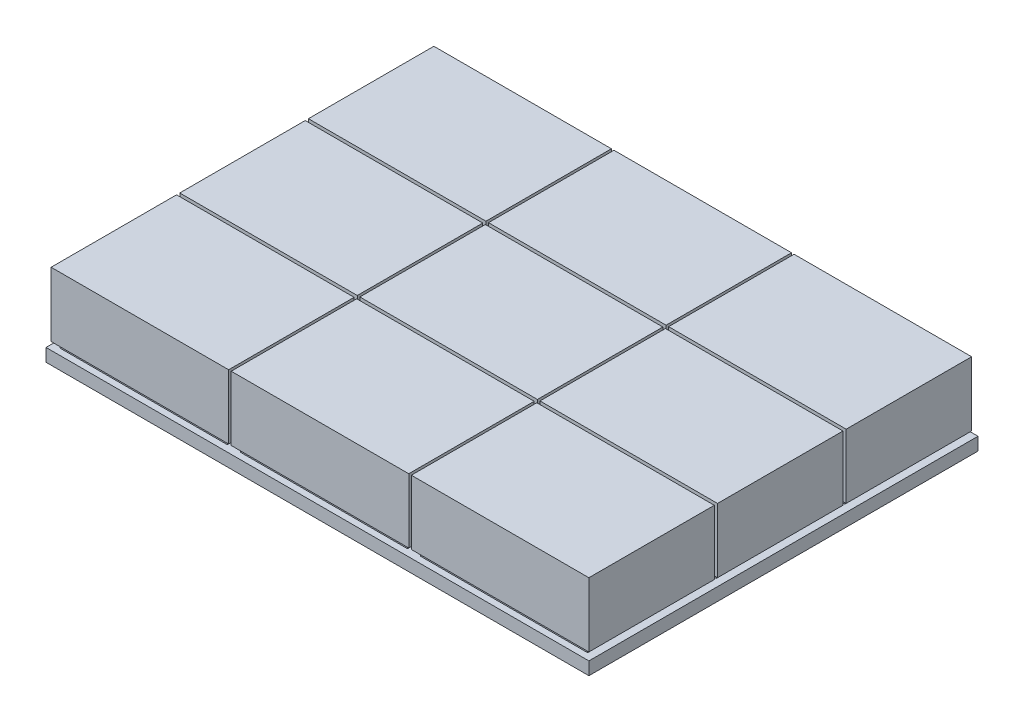
SolidWorks part; units mm, degrees
ref_plane "Front Plane" through (0, 0, 0) normal (0, 0, 1) x (1, 0, 0)
ref_plane "Top Plane" through (0, 0, 0) normal (0, 1, 0) x (1, 0, 0)
ref_plane "Right Plane" through (0, 0, 0) normal (1, 0, 0) x (0, 0, -1)
sketch "Sketch1" plane through (0, 0, 0) normal (0, 1, 0) x (1, 0, 0)
  line L1 (-35.5, -125) -> (35.5, -125)
  line L2 (-35.5, -125) -> (-35.5, 125)
  line L3 (-35.5, 125) -> (35.5, 125)
  line L4 (35.5, -125) -> (35.5, 125)
  line L5 (-35.5, -125) -> (35.5, 125) construction
  line L6 (-35.5, 125) -> (35.5, -125) construction
  point P0 (0, 0)
  dimension "D1" = 71
  dimension "D2" = 250
extrude "Boss-Extrude1" add sketch "Sketch1" along normal blind 5
sketch "Sketch2" plane through (0, 5, 0) normal (0, 1, 0) x (1, 0, 0)
  line L0 (0, 0) -> (0, -125) construction
  line L1 (-35.5, -125) -> (35.5, -125) construction
  line L3 (-32.5, -77.5) -> (32.5, -77.5)
  line L4 (-32.5, -77.5) -> (-32.5, -122.5)
  line L5 (-32.5, -122.5) -> (32.5, -122.5)
  line L6 (32.5, -77.5) -> (32.5, -122.5)
  line L7 (-32.5, -77.5) -> (32.5, -122.5) construction
  line L8 (-32.5, -122.5) -> (32.5, -77.5) construction
  point P5 (0, -100)
  dimension "D1" = 65
  dimension "D2" = 45
  dimension "D3" = 2.5
extrude "Boss-Extrude3" add sketch "Sketch2" along normal blind 2
pattern_linear "LPattern1" count 3 spacing 50 along (0, 0, -1) of "Boss-Extrude3"
sketch "Sketch3" plane through (0, 7, 0) normal (0, 1, 0) x (1, 0, 0)
  line L0 (0, 0) -> (0, -122.5) construction
  line L1 (-32.5, -122.5) -> (32.5, -122.5) construction
  line L2 (-35.5, 125) -> (-35.5, -125) construction
  line L3 (-34.5, -75.2576) -> (34.5, -75.2576)
  line L4 (-34.5, -75.2576) -> (-34.5, -124.0124)
  line L5 (-34.5, -124.0124) -> (34.5, -124.0124)
  line L6 (34.5, -75.2576) -> (34.5, -124.0124)
  line L7 (-34.5, -75.2576) -> (34.5, -124.0124) construction
  line L8 (-34.5, -124.0124) -> (34.5, -75.2576) construction
  point P5 (0, -99.635)
  dimension "D1" = 1
extrude "Boss-Extrude8" add sketch "Sketch3" along normal blind 25
pattern_linear "LPattern5" count 3 spacing 50 along (0, 0, -1) of "Boss-Extrude8"
sketch "Sketch5" plane through (0, 0, 0) normal (0, 1, 0) x (1, 0, 0)
  line L0 (0, 0) -> (208.2024, 0) construction
pattern_linear "LPattern6" count 3 spacing 70 along (1, 0, 0) of "Boss-Extrude1", "Boss-Extrude3", "LPattern1", "Boss-Extrude8", "LPattern5"
sketch "Sketch6" plane through (0, 5, 0) normal (0, 1, 0) x (1, 0, 0)
  line L5 (175.5, -125) -> (175.5, 125) construction
  line L6 (-35.5, 125) -> (175.5, 125)
  line L7 (-35.5, 125) -> (-35.5, 26.2217)
  line L8 (-35.5, 26.2217) -> (175.5, 26.2217)
  line L9 (175.5, 125) -> (175.5, 26.2217)
extrude "Cut-Extrude1" cut sketch "Sketch6" against normal blind 10
